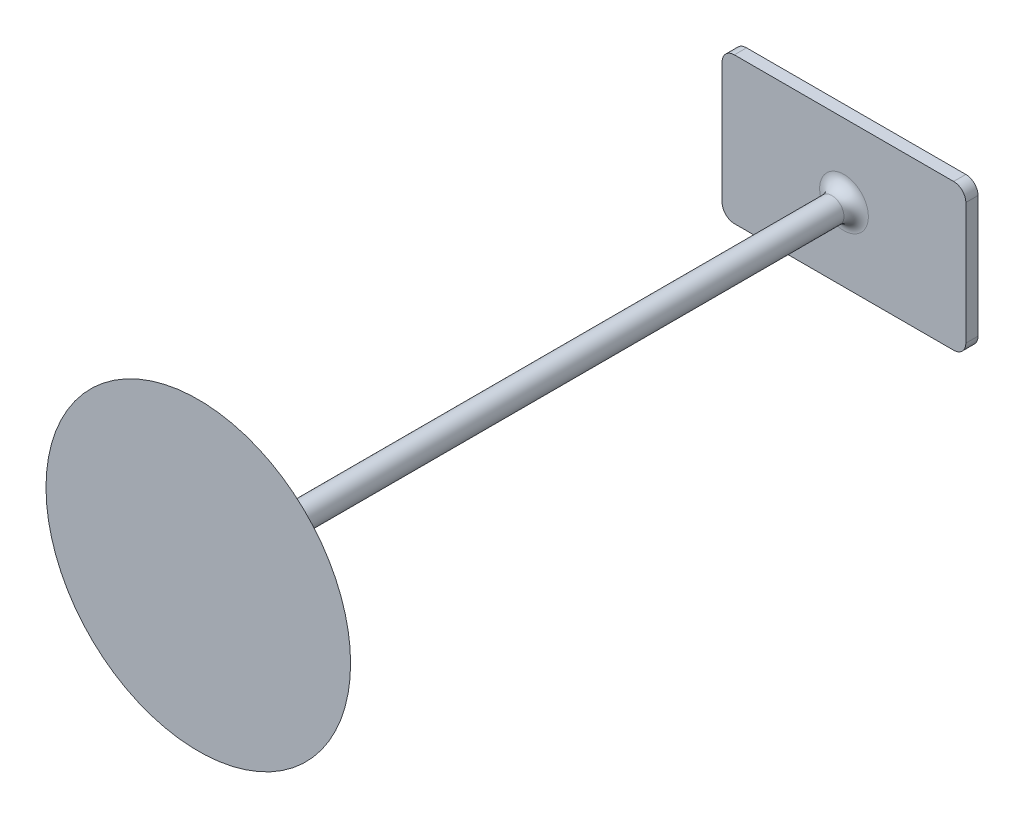
SolidWorks part; units mm, degrees
ref_plane "Front Plane" through (0, 0, 0) normal (0, 0, 1) x (1, 0, 0)
ref_plane "Top Plane" through (0, 0, 0) normal (0, 1, 0) x (1, 0, 0)
ref_plane "Right Plane" through (0, 0, 0) normal (1, 0, 0) x (0, 0, -1)
sketch "Sketch1" plane through (0, 0, 0) normal (0, 0, 1) x (1, 0, 0)
  line L1 (-9, 6) -> (9, 6)
  line L2 (-10, 5) -> (-10, -5)
  line L3 (-9, -6) -> (9, -6)
  line L4 (10, 5) -> (10, -5)
  line L5 (-10, 6) -> (10, -6) construction
  line L6 (-10, -6) -> (10, 6) construction
  arc A0 (9, 6) -> (10, 5) centre (9, 5) cw
  arc A1 (-10, -5) -> (-9, -6) centre (-9, -5) ccw
  arc A2 (-9, 6) -> (-10, 5) centre (-9, 5) ccw
  arc A3 (9, -6) -> (10, -5) centre (9, -5) ccw
  point P0 (0, 0)
  dimension "D2" = 1
  dimension "D1" = 12
  dimension "20" = 20
extrude "Boss-Extrude1" add sketch "Sketch1" along normal blind 1
sketch "Sketch2" plane through (0, 0, 0) normal (0, 1, 0) x (1, 0, 0)
  line L0 (0, -1) -> (0, -54)
  line L1 (9, -1) -> (-9, -1) construction
  line L2 (0, -54) -> (12.5, -54)
  line L4 (1, -51.3) -> (1, -1)
  line L5 (1, -1) -> (0, -1)
  line L6 (9, 0) -> (-9, 0) construction
  arc A0 (12.5, -54) -> (1, -51.3) centre (-24.9922, -187.8482) ccw
  dimension "D3" = 139
  dimension "D1" = 12.5
  dimension "D2" = 1
  dimension "D4" = 2.7
  dimension "D5" = 54
revolve "Revolve2" add sketch "Sketch2" angle 360 about L0
fillet "Fillet1" radius 2 1 edges at (-1, 0, 51.3)
fillet "Fillet2" radius 1 1 edges at (-1, 0, 1)
